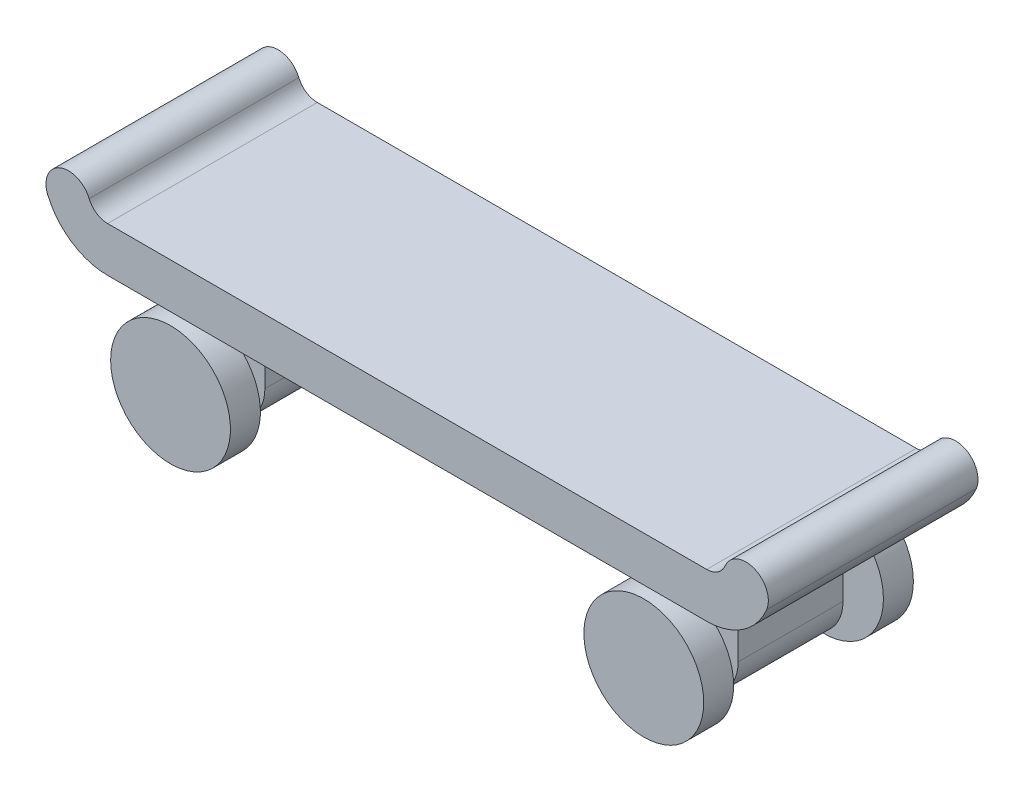
SolidWorks part; units mm, degrees
ref_plane "Alzado" through (0, 0, 0) normal (0, 0, 1) x (1, 0, 0)
ref_plane "Planta" through (0, 0, 0) normal (0, 1, 0) x (1, 0, 0)
ref_plane "Vista lateral" through (0, 0, 0) normal (1, 0, 0) x (0, 0, -1)
sketch "Sketch1" plane through (0, 0, 0) normal (0, 0, 1) x (1, 0, 0)
  line L0 (-20, 0) -> (20, 0)
  line L1 (0, 0) -> (0, 10.5498) construction
  line L2 (-20, 3) -> (20, 3)
  arc A0 (20, 0) -> (24, 2.6667) centre (20, 4.3333) ccw
  arc A1 (-20, 0) -> (-24, 2.6667) centre (-20, 4.3333) cw
  arc A2 (-20, 3) -> (-21.2308, 3.8205) centre (-20, 4.3333) cw
  arc A3 (20, 3) -> (21.2308, 3.8205) centre (20, 4.3333) ccw
  arc A4 (-24, 2.6667) -> (-21.2308, 3.8205) centre (-22.6154, 3.2436) cw
  arc A5 (24, 2.6667) -> (21.2308, 3.8205) centre (22.6154, 3.2436) ccw
extrude "Boss-Extrude1" add sketch "Sketch1" along normal mid plane 14
sketch "Sketch2" plane through (0, 0, 0) normal (0, 0, 1) x (1, 0, 0)
  line L0 (0, 0) -> (0, 15.0418) construction
  line L1 (18.6, 0) -> (18.6, -4.8)
  line L2 (-20, 0) -> (20, 0) construction
  line L3 (13, -4.8) -> (13, 0)
  line L4 (13, 0) -> (18.6, 0)
  line L5 (-13, 0) -> (-18.6, 0)
  line L6 (-13, -4.8) -> (-13, 0)
  line L7 (-18.6, 0) -> (-18.6, -4.8)
  arc A0 (18.6, -4.8) -> (13, -4.8) centre (15.8, -4.8) cw
  circle A1 centre (15.8, -4.8) radius 1.75
  circle A2 centre (-15.8, -4.8) radius 1.75
  arc A3 (-18.6, -4.8) -> (-13, -4.8) centre (-15.8, -4.8) ccw
extrude "Boss-Extrude2" add sketch "Sketch2" along normal mid plane 7
sketch "Sketch3" plane through (0, 0, 0) normal (0, 0, 1) x (1, 0, 0)
  line L0 (0, 0) -> (0, 13.819) construction
  circle A0 centre (15.8, -4.8) radius 1.15
  circle A1 centre (-15.8, -4.8) radius 1.15
  circle A4 centre (15.8, -4.8) radius 1.75 construction
  dimension "D1" = 0.6
extrude "Boss-Extrude3" add sketch "Sketch3" along normal mid plane 10 separate body
sketch "Sketch4" plane through (0, 0, 5) normal (0, 0, 1) x (1, 0, 0)
  line L0 (0, 0) -> (0, 12.154) construction
  circle A0 centre (15.8, -4.8) radius 4
  circle A1 centre (-15.8, -4.8) radius 4
extrude "Boss-Extrude4" add sketch "Sketch4" along normal blind 2
mirror "Mirror1" about plane through (0, 0, 0) normal (0, 0, 1) of "Boss-Extrude4"
equation "\"Length\"= 40"
equation "\"Width\"=10"
equation "\"Height\"= 8"
equation "\"D1@Sketch1\"=\"Length\""
equation "\"D2@Sketch1\"=\"Height\"/3"
equation "\"D3@Sketch1\"=\"Height\"/2"
equation "\"D1@Boss-Extrude1\"=\"Width\"+\"Height\"*0.5mm"
equation "\"D1@Sketch2\"=\"Length\"*0.65"
equation "\"D2@Sketch2\"=\"Height\"*0.6"
equation "\"D3@Sketch2\"=\"Height\"*0.25 +0.8"
equation "\"D4@Sketch2\"=\"Height\"*0.25 +1.5"
equation "\"D1@Boss-Extrude2\"=\"Width\"*0.7"
equation "\"D1@Boss-Extrude3\"=\"Width\""
equation "\"D1@Sketch4\"=\"Height\""
equation "\"D1@Boss-Extrude4\"=\"Height\"*0.25"
